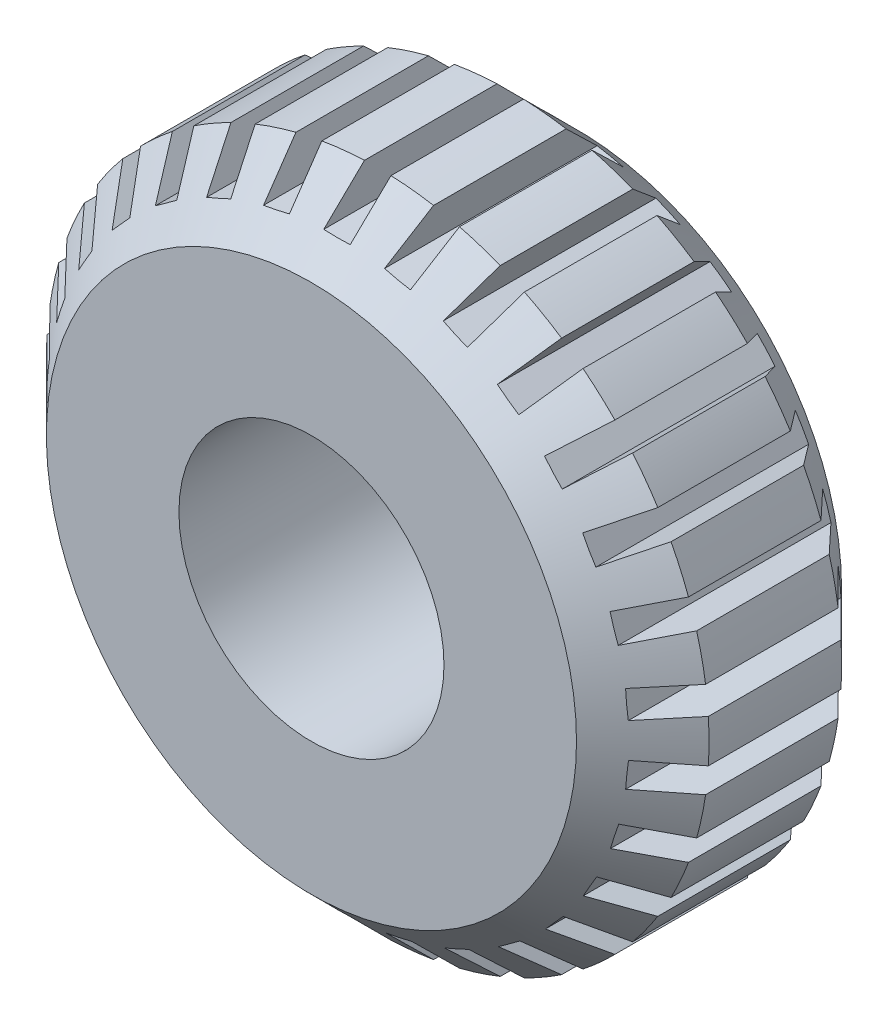
SolidWorks part; units mm, degrees
ref_plane "Front Plane" through (0, 0, 0) normal (0, 0, 1) x (1, 0, 0)
ref_plane "Top Plane" through (0, 0, 0) normal (0, 1, 0) x (1, 0, 0)
ref_plane "Right Plane" through (0, 0, 0) normal (1, 0, 0) x (0, 0, -1)
sketch "Sketch1" plane through (0, 0, 0) normal (0, 0, 1) x (1, 0, 0)
  line L0 (-67.1709, 0) -> (68.8323, 0) construction
  circle A0 centre (0.8307, 0) radius 50
  circle A1 centre (0.8307, 0) radius 20
  dimension "D1" = 100
  dimension "D2" = 40
extrude "Boss-Extrude6" add sketch "Sketch1" along normal blind 40
chamfer "Chamfer9" distance 10 angle 45 2 edges at (50.8307, 0, 0) (50.8307, 0, 40)
sketch "Sketch5" plane through (0, 0, 0) normal (0, 0, 1) x (1, 0, 0)
  line L1 (2.7297, 43.9072) -> (2.8304, 49.9668)
  line L2 (-1.2708, 43.9072) -> (-1.1702, 49.9599)
  line L3 (-1.2708, 43.9072) -> (2.7297, 43.9072)
  circle A0 centre (0.8307, 0) radius 50 construction
  arc A1 (2.8303, 49.96) -> (-1.1702, 49.9599) centre (0.8307, 0) ccw
  point P0 (0, 0)
  point P1 (0.8307, 50)
  point P5 (1.9997, -0.0332)
  point P7 (-1.9997, 0.0332)
  point P8 (-1.169, 50.0332)
extrude "Cut-Extrude5" cut sketch "Sketch5" along normal blind 40 contours L1 A1 L2 L3
pattern_circular "CirPattern5" count 30 over 360 about axis through (0.8307, 0, 0) along (0, 0, 1) of "Cut-Extrude5"
